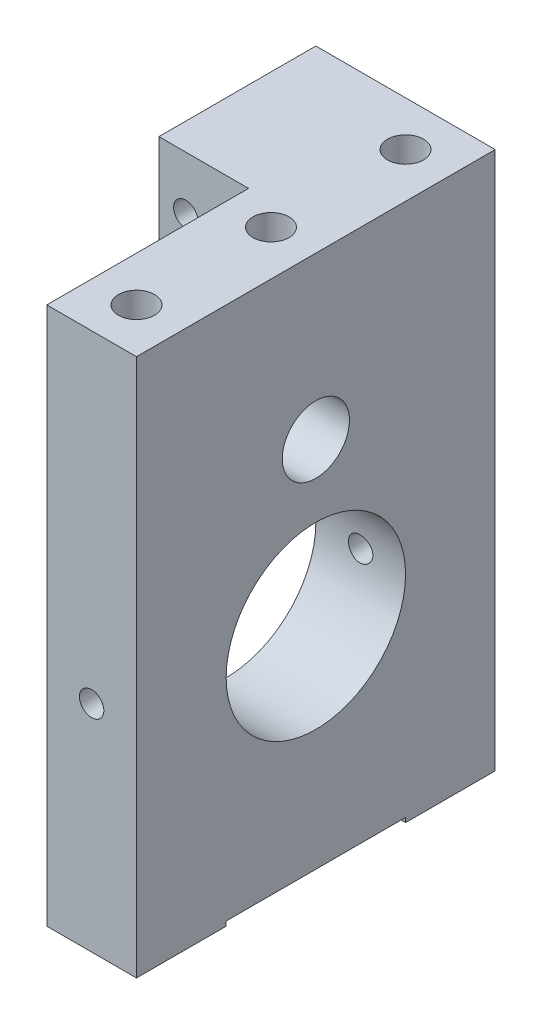
SolidWorks part; units mm, degrees
ref_plane "Front Plane" through (0, 0, 0) normal (0, 0, 1) x (1, 0, 0)
ref_plane "Top Plane" through (0, 0, 0) normal (0, 1, 0) x (1, 0, 0)
ref_plane "Right Plane" through (0, 0, 0) normal (1, 0, 0) x (0, 0, -1)
sketch "Sketch1" plane through (0, 0, 0) normal (1, 0, 0) x (0, 0, -1)
  line L1 (-25.4, 38.1) -> (25.4, 38.1)
  line L2 (-25.4, 38.1) -> (-25.4, -38.1)
  line L3 (-25.4, -38.1) -> (25.4, -38.1)
  line L4 (25.4, 38.1) -> (25.4, -38.1)
  dimension "D1" = 25.4
  dimension "D2" = 25.4
  dimension "D3" = 38.1
  dimension "D4" = 38.1
extrude "Boss-Extrude1" add sketch "Sketch1" along normal mid plane 12.7
hole_wizard "1/4-20 Tapped Hole1" positions "Sketch4" profile "Sketch3" tap size "1/4-20" standard "ANSI Inch"
sketch "Sketch4" plane through (0, -38.1, 0) normal (0, -1, 0) x (-1, 0, 0)
  point P0 (0, -19.05)
  point P2 (0, 19.05)
  dimension "D1" = 19.05
  dimension "D2" = 19.05
sketch "Sketch3" plane through (0, -38.1, 19.05) normal (1, 0, 0) x (0, 0, -1)
  line L0 (0, 0) -> (0, 20.5838)
  line L1 (0, 20.5838) -> (2.5527, 19.05)
  line L2 (2.5527, 19.05) -> (2.5527, 0)
  line L5 (2.5527, 0) -> (0, 0)
  line L10 (0, 20.5838) -> (-2.5527, 19.05) construction
  line L11 (0, -6.35) -> (0, 107.95) construction
  dimension "Tap Drill Dia." = 5.1054
  dimension "Tap Drill Depth" = 19.05
  dimension "Drill Angle" = 118
cosmetic thread "Hole Thread1" parameters "D1"=12.7, "D2"=6.35
cosmetic thread "Hole Thread2" parameters "D1"=12.7, "D2"=6.35
sketch "Sketch5" plane through (6.35, 0, 0) normal (1, 0, 0) x (0, 0, -1)
  line L0 (-25.4, -38.1) -> (25.4, -38.1) construction
  line L1 (-12.7, -38.1) -> (12.7, -38.1)
  line L2 (-12.7, -38.1) -> (-12.7, -37.465)
  line L3 (-12.7, -37.465) -> (12.7, -37.465)
  line L4 (12.7, -38.1) -> (12.7, -37.465)
  dimension "D1" = 12.7
  dimension "D2" = 12.7
  dimension "D3" = 0.635
extrude "Cut-Extrude1" cut sketch "Sketch5" against normal up to next
hole_wizard "1/4-20 Tapped Hole2" positions "Sketch7" profile "Sketch6" tap size "1/4-20" standard "ANSI Inch"
sketch "Sketch7" plane through (0, 38.1, 0) normal (0, 1, 0) x (1, 0, 0)
  point P0 (0, 19.05)
  point P2 (0, 0)
  point P5 (0, -19.05)
  dimension "D1" = 19.05
  dimension "D2" = 19.05
sketch "Sketch6" plane through (0, 38.1, -19.05) normal (1, 0, 0) x (0, 0, 1)
  line L0 (0, 0) -> (0, 20.5838)
  line L1 (0, 20.5838) -> (2.5527, 19.05)
  line L2 (2.5527, 19.05) -> (2.5527, 0)
  line L5 (2.5527, 0) -> (0, 0)
  line L10 (0, 20.5838) -> (-2.5527, 19.05) construction
  line L11 (0, -6.35) -> (0, 107.95) construction
  dimension "Tap Drill Dia." = 5.1054
  dimension "Tap Drill Depth" = 19.05
  dimension "Drill Angle" = 118
cosmetic thread "Hole Thread3" parameters "D1"=12.7, "D2"=6.35
cosmetic thread "Hole Thread4" parameters "D1"=12.7, "D2"=6.35
cosmetic thread "Hole Thread5" parameters "D1"=12.7, "D2"=6.35
sketch "Sketch8" plane through (6.35, 0, 0) normal (1, 0, 0) x (0, 0, -1)
  line L0 (-25.4, -38.1) -> (-12.7, -38.1) construction
  circle A0 centre (0, -7.62) radius 12.7
  dimension "D1" = 30.48
extrude "Cut-Extrude2" cut sketch "Sketch8" against normal up to next
sketch "Sketch9" plane through (-6.35, 0, 0) normal (-1, 0, 0) x (0, 0, 1)
  line L1 (-25.4, 38.1) -> (-3.175, 38.1)
  line L2 (-25.4, 38.1) -> (-25.4, 19.05)
  line L3 (-25.4, 19.05) -> (-3.175, 19.05)
  line L4 (-3.175, 38.1) -> (-3.175, 19.05)
  dimension "D1" = 3.175
  dimension "D2" = 19.05
extrude "Boss-Extrude2" add sketch "Sketch9" along normal blind 12.7
hole_wizard "#8-32 Tapped Hole1" positions "Sketch11" profile "Sketch10" tap size "#8-32" standard "ANSI Inch" end condition through all
sketch "Sketch11" plane through (0, 0, -3.175) normal (0, 0, 1) x (1, 0, 0)
  line L0 (-19.05, 19.05) -> (-6.35, 19.05) construction
  line L1 (-19.05, 19.05) -> (-19.05, 38.1) construction
  point P0 (-15.24, 30.48)
  dimension "D1" = 11.43
  dimension "D2" = 3.81
cosmetic thread "Hole Thread6" parameters "D2"=4.1656
sketch "Sketch10" plane through (-15.24, 30.48, -3.175) normal (1, 0, 0) x (0, -1, 0)
  line L0 (0, 0) -> (0, 22.225)
  line L1 (0, 22.225) -> (1.7272, 22.225)
  line L2 (1.7272, 22.225) -> (1.7272, 0)
  line L5 (1.7272, 0) -> (0, 0)
  line L11 (0, -6.35) -> (0, 107.95) construction
  dimension "Thru Tap Drill Dia." = 3.4544
  dimension "Thru Tap Drill Depth" = 22.225
sketch "Sketch12" plane through (6.35, 0, 0) normal (1, 0, 0) x (0, 0, -1)
  circle A0 centre (0, 15.24) radius 4.7625
  dimension "D1" = 15.24
extrude "Cut-Extrude3" cut sketch "Sketch12" against normal through all
hole_wizard "#8-32 Tapped Hole2" positions "Sketch14" profile "Sketch13" tap size "#8-32" standard "ANSI Inch" end condition through all
sketch "Sketch14" plane through (0, 0, 25.4) normal (0, 0, 1) x (1, 0, 0)
  line L0 (6.35, -38.1) -> (-6.35, -38.1) construction
  point P0 (0, -7.62)
  dimension "D1" = 30.48
cosmetic thread "Hole Thread7" parameters "D2"=4.1656
sketch "Sketch13" plane through (0, -7.62, 25.4) normal (1, 0, 0) x (0, -1, 0)
  line L0 (0, 0) -> (0, 50.8)
  line L1 (0, 50.8) -> (1.7272, 50.8)
  line L2 (1.7272, 50.8) -> (1.7272, 0)
  line L5 (1.7272, 0) -> (0, 0)
  line L11 (0, -6.35) -> (0, 107.95) construction
  dimension "Thru Tap Drill Dia." = 3.4544
  dimension "Thru Tap Drill Depth" = 50.8
